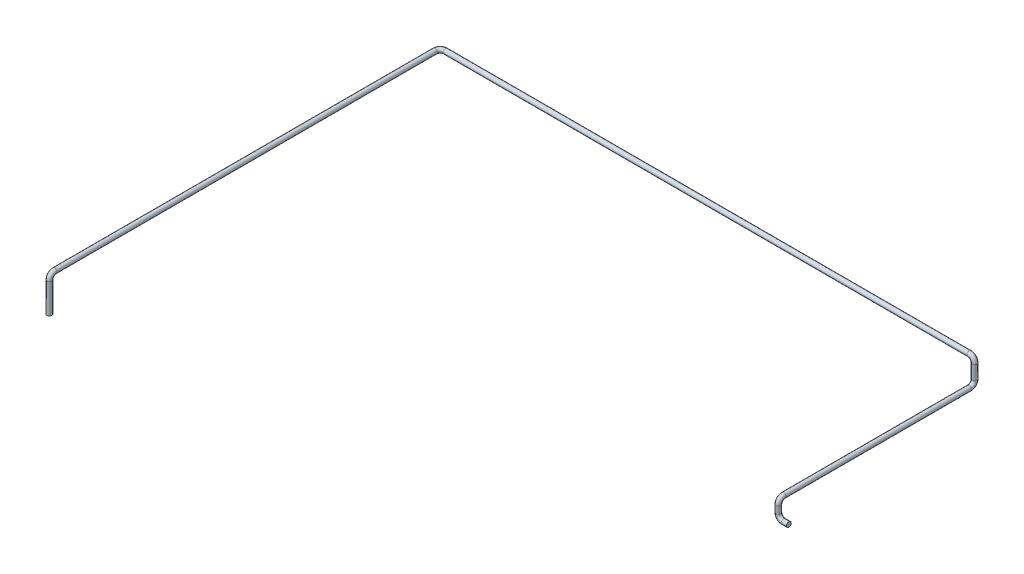
SolidWorks part; units mm, degrees
ref_plane "Alzado" through (0, 0, 0) normal (0, 0, 1) x (1, 0, 0)
ref_plane "Planta" through (0, 0, 0) normal (0, 1, 0) x (1, 0, 0)
ref_plane "Vista lateral" through (0, 0, 0) normal (1, 0, 0) x (0, 0, -1)
sketch3d "Croquis3D1"
  line L0 (0, 0, 0) -> (-30, 0, 0)
  line L1 (-60, 30, 0) -> (-60, 70, 0)
  line L2 (-60, 100, -30) -> (-60, 100, -1090)
  line L6 (-60, 130, -1120) -> (-60, 210, -1120)
  line L7 (-90, 240, -1120) -> (-3080, 240, -1120)
  line L8 (-3110, 240, -1090) -> (-3110, 240, 1080)
  line L9 (-3110, 210, 1110) -> (-3110, 40, 1110)
  arc A0 (-3110, 240, 1080) -> (-3110, 210, 1110) centre (-3110, 210, 1080) ccw
  arc A1 (-3080, 240, -1120) -> (-3110, 240, -1090) centre (-3080, 240, -1090) ccw
  arc A2 (-60, 210, -1120) -> (-90, 240, -1120) centre (-90, 210, -1120) ccw
  arc A3 (-60, 130, -1120) -> (-60, 100, -1090) centre (-60, 130, -1090) ccw
  arc A4 (-60, 70, 0) -> (-60, 100, -30) centre (-60, 70, -30) ccw
  arc A5 (-30, 0, 0) -> (-60, 30, 0) centre (-30, 30, 0) ccw
  point P6 (-3110, 240, 1110)
  point P11 (-3080, 210, 1080)
  point P15 (-3110, 240, -1120)
  point P16 (-3080, 270, -1090)
  point P19 (-60, 240, -1120)
  point P20 (-90, 210, -1090)
  point P23 (-60, 100, -1120)
  point P24 (-90, 130, -1090)
  point P27 (-60, 100, 0)
  point P28 (-90, 70, -30)
  point P31 (-60, 0, 0)
  point P32 (-30, 30, -30)
  dimension "D8" = 30
  dimension "D1" = 60
  dimension "D2" = 100
  dimension "D3" = 1120
  dimension "D4" = 140
  dimension "D5" = 3050
  dimension "D6" = 2230
  dimension "D7" = 200
sketch "Croquis1" plane through (0, 0, 0) normal (1, 0, 0) x (0, 0, -1)
  circle A0 centre (0, 0) radius 13.7
  dimension "D1" = 27.4
sweep "Barrer1" add profiles "Croquis1" path "Croquis3D1"
